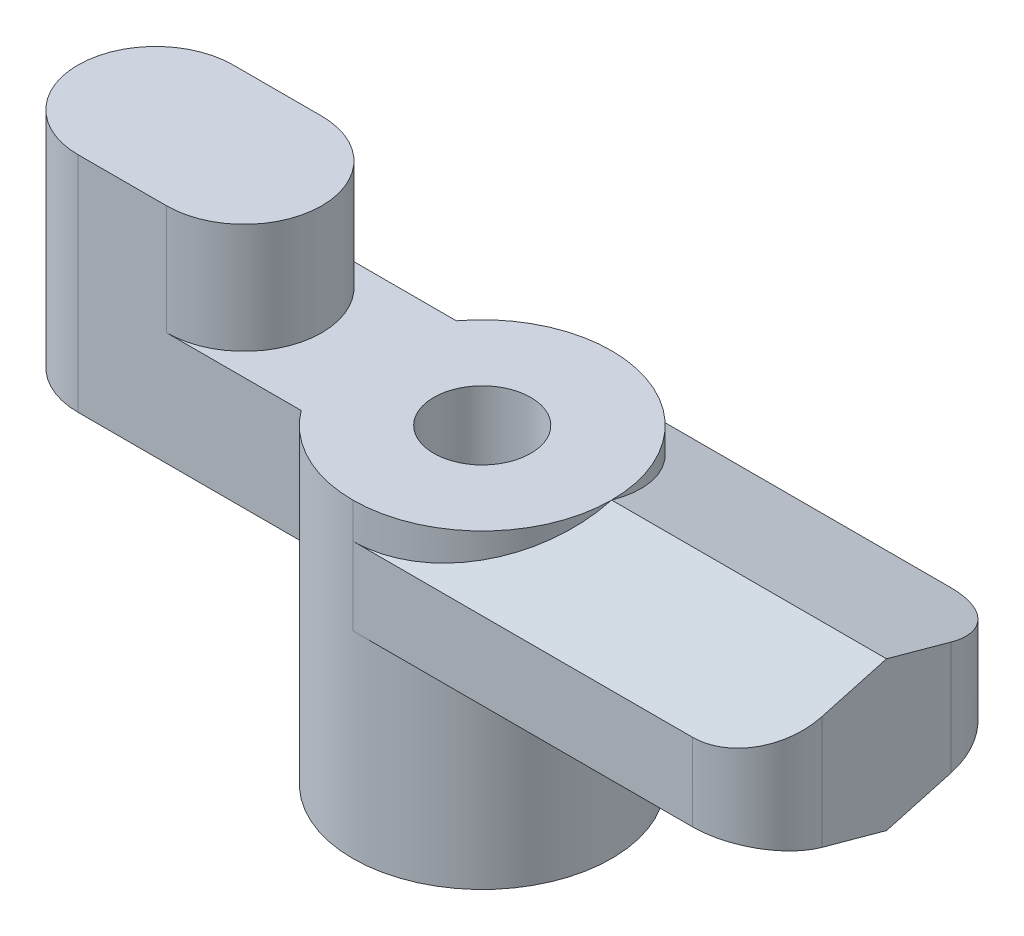
SolidWorks part; units mm, degrees
material "Nylon 101"
ref_plane "Front" through (0, 0, 0) normal (0, 0, 1) x (1, 0, 0)
ref_plane "Top" through (0, 0, 0) normal (0, 1, 0) x (1, 0, 0)
ref_plane "Right" through (0, 0, 0) normal (1, 0, 0) x (0, 0, -1)
sketch "Sketch7" plane through (0, 0, 0) normal (0, 0, 1) x (1, 0, 0)
  line L0 (-19.8438, 0) -> (19.8438, 0) construction
  point P2 (0, 0)
  dimension "A" = 39.6875
sketch "Sketch1" plane through (0, 0, 0) normal (0, 1, 0) x (1, 0, 0)
  circle A1 centre (0, 0) radius 6.35
  dimension "D2" = 12.7
extrude "Boss-Extrude1" add sketch "Sketch1" along normal blind 15.24
sketch "Sketch2" plane through (0, 0, 0) normal (1, 0, 0) x (0, 0, -1)
  line L0 (-6.35, 9.6837) -> (-6.35, 13.4937)
  line L1 (-6.35, 15.24) -> (-6.35, 0) construction
  line L2 (-6.35, 13.4937) -> (0, 15.24)
  line L3 (0, 15.24) -> (6.35, 13.4937)
  line L4 (6.35, 0) -> (6.35, 15.24) construction
  line L5 (6.35, 13.4937) -> (6.35, 9.6837)
  line L6 (-6.35, 15.24) -> (-6.35, 0) construction
  line L7 (-6.35, 15.24) -> (-6.35, 0) construction
  line L8 (6.35, 15.24) -> (-6.35, 15.24) construction
  line L9 (-6.35, 9.6837) -> (0, 7.9375)
  line L10 (0, 7.9375) -> (6.35, 9.6837)
  dimension "D1" = 3.81
  dimension "D2" = 7.9375
extrude "Boss-Extrude2" add sketch "Sketch2" along normal up to vertex (19.8438 mm away) up to point (19.8438, 0, 0)
fillet "Fillet1" radius 3.175 2 edges at (19.8438, 11.5887, -6.35) (19.8438, 11.5887, 6.35)
sketch "Sketch3" plane through (0, 0, 0) normal (0, -1, 0) x (1, 0, 0)
  circle A0 centre (0, 0) radius 2.3813
  dimension "D1" = 4.7625
extrude "Cut-Extrude1" cut sketch "Sketch3" against normal through all
sketch "Sketch4" plane through (0, 15.24, 0) normal (0, 1, 0) x (1, 0, 0)
  line L0 (-6.35, 0) -> (-16.0338, 0) construction
  line L1 (-5.08, -3.81) -> (-16.0338, -3.81)
  line L2 (-5.08, 3.81) -> (-16.0338, 3.81)
  line L3 (-16.0338, 0) -> (-19.8438, 0) construction
  arc A1 (-16.0338, 3.81) -> (-16.0338, -3.81) centre (-16.0338, 0) ccw
  circle A3 centre (0, 0) radius 6.35
  arc A4 (-5.08, 3.81) -> (-5.08, -3.81) centre (0, 0) ccw
  dimension "D2" = 7.62
  dimension "D1" = 0
extrude "Boss-Extrude3" add sketch "Sketch4" against normal up to vertex (5.5563 mm away)
sketch "Sketch5" plane through (0, 15.24, 0) normal (0, 1, 0) x (1, 0, 0)
  line L0 (-16.0338, 0) -> (-11.684, 0) construction
  line L1 (-16.0338, 3.81) -> (-11.684, 3.81)
  line L2 (-16.0338, -3.81) -> (-11.684, -3.81)
  line L3 (-6.35, 0) -> (-7.874, 0) construction
  arc A0 (-16.0338, 3.81) -> (-16.0338, -3.81) centre (-16.0338, 0) ccw
  arc A1 (-11.684, -3.81) -> (-11.684, 3.81) centre (-11.684, 0) ccw
  arc A2 (-16.0338, 3.81) -> (-16.0338, -3.81) centre (-16.0338, 0) ccw construction
  point P4 (-13.8589, 0)
  dimension "D1" = 1.524
sketch "Sketch6" plane through (0, 0, 0) normal (0, 0, 1) x (1, 0, 0)
  line L0 (0, 0) -> (0, 20.6375) construction
  dimension "D1" = 20.6375
extrude "Boss-Extrude4" add sketch "Sketch5" along normal up to vertex (5.3975 mm away) up to point (0, 20.6375, 0)
